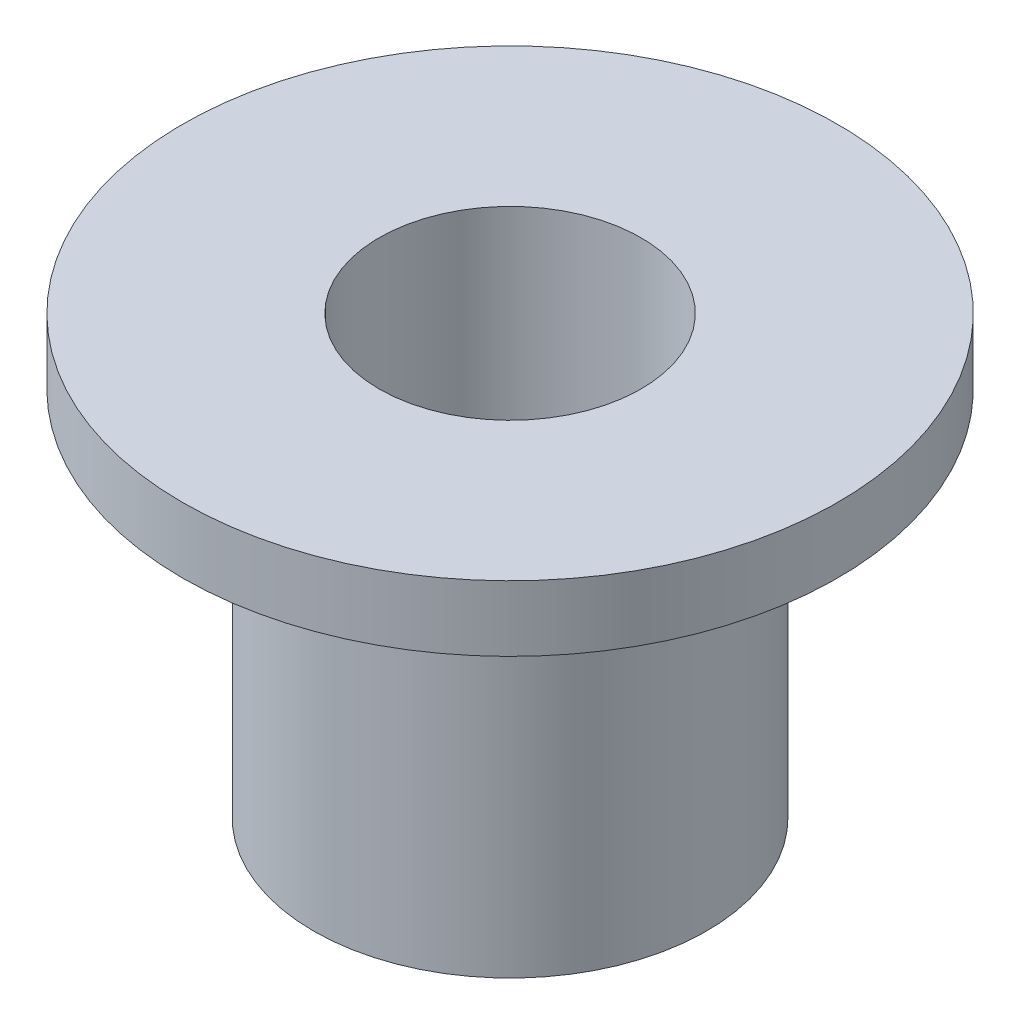
SolidWorks part; units mm, degrees
material "Nylon 101"
ref_plane "Plan de face" through (0, 0, 0) normal (0, 0, 1) x (1, 0, 0)
ref_plane "Plan de dessus" through (0, 0, 0) normal (0, 1, 0) x (1, 0, 0)
ref_plane "Plan de droite" through (0, 0, 0) normal (1, 0, 0) x (0, 0, -1)
sketch "Esquisse1" plane through (0, 0, 0) normal (0, 0, 1) x (1, 0, 0)
  line L0 (0, 5) -> (0, 0) construction
  line L1 (-3.75, 5) -> (-1.5, 5)
  line L2 (-1.5, 5) -> (-1.5, 0)
  line L3 (-1.5, 0) -> (-2.25, 0)
  line L4 (-2.25, 0) -> (-2.25, 4.25)
  line L5 (-2.25, 4.25) -> (-3.75, 4.25)
  line L6 (-3.75, 4.25) -> (-3.75, 5)
  line L7 (0, 0) -> (-2.25, 0) construction
  dimension "D1" = 1.5
  dimension "D2" = 0
  dimension "D3" = 2.25
  dimension "D4" = 3.75
  dimension "D5" = 0.75
  dimension "D6" = 5
revolve "Révolution1" add sketch "Esquisse1" angle 360 about L0
